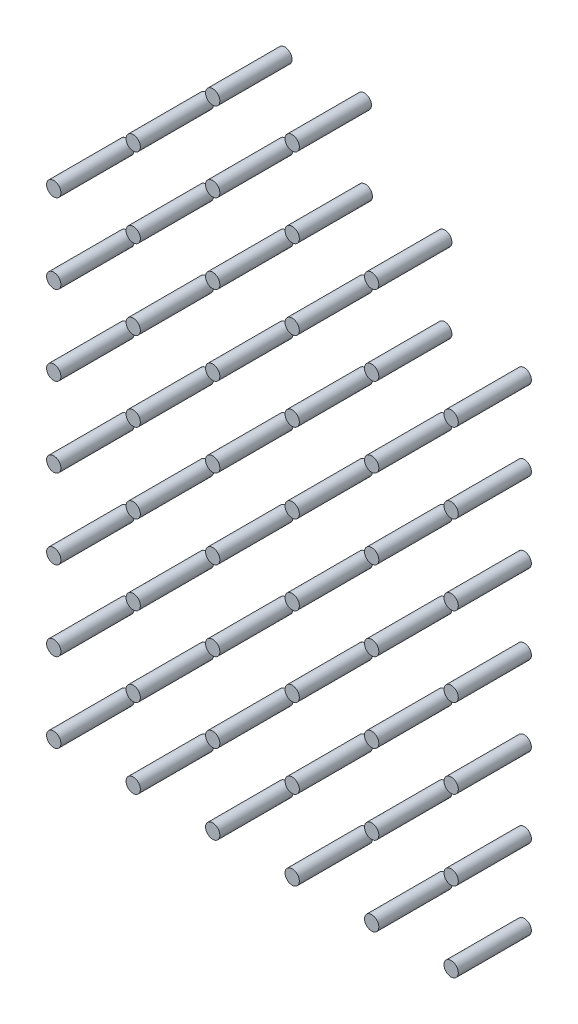
SolidWorks part; units mm, degrees
ref_plane "前视基准面" through (0, 0, 0) normal (0, 0, 1) x (1, 0, 0)
ref_plane "上视基准面" through (0, 0, 0) normal (0, 1, 0) x (1, 0, 0)
ref_plane "右视基准面" through (0, 0, 0) normal (1, 0, 0) x (0, 0, -1)
other "Configuration Table"
sketch "草图1" plane through (0, 0, 0) normal (0, 0, 1) x (1, 0, 0)
  circle A0 centre (0, 0) radius 0.225
  dimension "D1" = 0.45
extrude "凸台-拉伸1" add sketch "草图1" along normal blind 2.3
pattern_linear "阵列(线性)1" count 8 spacing 2.5 along (0, 1, 0) count 7 spacing 2.5 along (1, 0, 0)
pattern_linear "阵列(线性)2" count 2 spacing 2.5 along (0, 1, 0)
sketch "草图2" plane through (0, 0, 2.3) normal (0, 0, 1) x (1, 0, 0)
  line L0 (7.275, 20) -> (7.5, 20) construction
  line L1 (7.5, 20) -> (7.5, 19.775) construction
  circle A0 centre (7.5, 20) radius 0.225 construction
delete or keep bodies "实体-删除/保留 1" type keep bodies bodies 130 147 107 124 141 118 135 112 129 146 106 123 140 117 134 151 111 128 145 122 139 116 133 150 110 127 144 171 121 138 115 132 149 109 126 143 172 120 137 114
sketch "草图3" plane through (0, 0, 0) normal (0, 0, -1) x (-1, 0, 0)
  line L1 (-8.8798, 21.1689) -> (-4.1427, 21.1689)
  line L2 (-8.8798, 21.1689) -> (-8.8798, 19.5298)
  line L3 (-8.8798, 19.5298) -> (-4.1427, 19.5298)
  line L4 (-4.1427, 21.1689) -> (-4.1427, 19.5298)
extrude "切除-拉伸1" cut sketch "草图3" against normal blind 0.03
